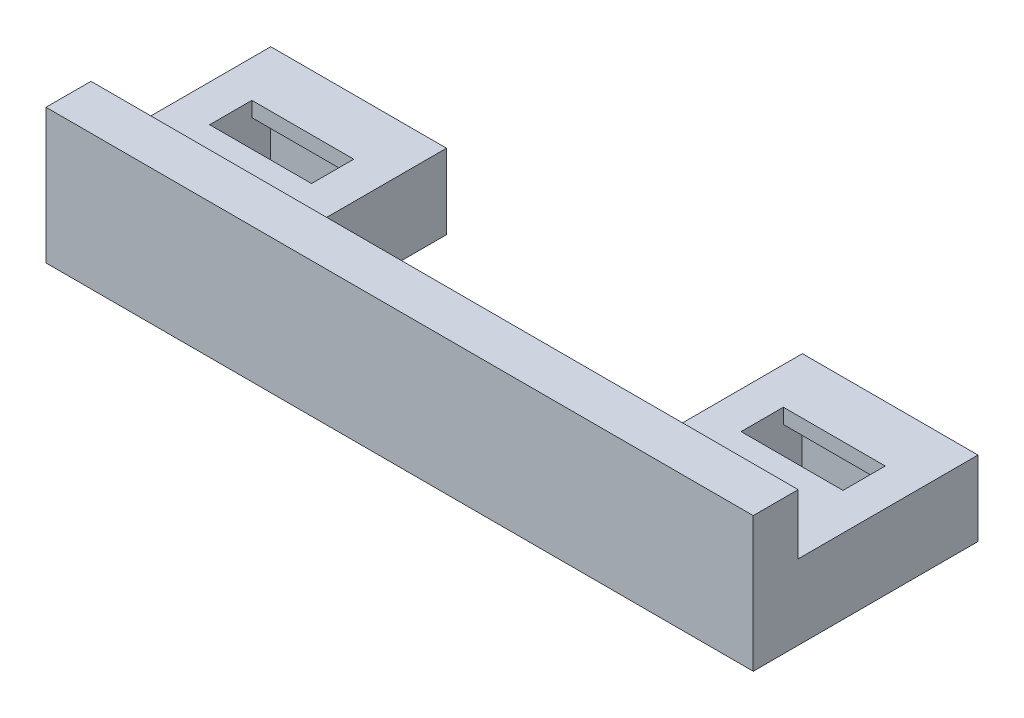
SolidWorks part; units mm, degrees
ref_plane "Front Plane" through (0, 0, 0) normal (0, 0, 1) x (1, 0, 0)
ref_plane "Top Plane" through (0, 0, 0) normal (0, 1, 0) x (1, 0, 0)
ref_plane "Right Plane" through (0, 0, 0) normal (1, 0, 0) x (0, 0, -1)
sketch "Sketch1" plane through (0, 0, 0) normal (0, 1, 0) x (1, 0, 0)
  line L1 (-59.4224, 28.5586) -> (0.5216, 28.5586)
  line L2 (-59.4224, 28.5586) -> (-59.4224, 9.5086)
  line L3 (-59.4224, 9.5086) -> (0.5216, 9.5086)
  line L4 (0.5216, 28.5586) -> (0.5216, 9.5086)
  line L13 (-47.6495, 18.6526) -> (-56.2855, 18.6526)
  line L14 (-47.6495, 18.6526) -> (-47.6495, 25.409)
  line L15 (-47.6495, 25.409) -> (-56.2855, 25.409)
  line L16 (-56.2855, 18.6526) -> (-56.2855, 25.409)
  line L17 (-11.2386, 18.6526) -> (-2.6026, 18.6526)
  line L18 (-11.2386, 18.6526) -> (-11.2386, 25.409)
  line L19 (-11.2386, 25.409) -> (-2.6026, 25.409)
  line L20 (-2.6026, 18.6526) -> (-2.6026, 25.409)
  dimension "D1" = 59.944
  dimension "D2" = 19.05
extrude "Boss-Extrude1" add sketch "Sketch1" along normal blind 5.08
sketch "Sketch2" plane through (0, 5.08, 0) normal (0, 1, 0) x (1, 0, 0)
  line L1 (-59.4224, 9.5086) -> (0.5216, 9.5086)
  line L2 (-59.4224, 9.5086) -> (-59.4224, 28.5586)
  line L3 (-59.4224, 28.5586) -> (0.5216, 28.5586)
  line L4 (0.5216, 9.5086) -> (0.5216, 28.5586)
  line L5 (-56.2855, 25.409) -> (-56.2855, 18.6526) construction
  line L6 (-56.2855, 23.8215) -> (-47.6495, 23.8215)
  line L7 (-56.2855, 23.8215) -> (-56.2855, 20.2401)
  line L8 (-11.2386, 25.409) -> (-11.2386, 18.6526) construction
  line L9 (-56.2855, 20.2401) -> (-47.6495, 20.2401)
  line L19 (-47.6495, 23.8215) -> (-47.6495, 20.2401)
  line L28 (-11.2386, 23.8215) -> (-2.6026, 23.8215)
  line L29 (-11.2386, 23.8215) -> (-11.2386, 20.2401)
  line L30 (-11.2386, 20.2401) -> (-2.6026, 20.2401)
  line L31 (-2.6026, 23.8215) -> (-2.6026, 20.2401)
extrude "Boss-Extrude2" add sketch "Sketch2" along normal blind 1.27
sketch "Sketch4" plane through (0, 0, 0) normal (0, -1, 0) x (1, 0, 0)
  line L5 (-9.5664, -25.0308) -> (-4.2749, -25.0308)
  line L6 (-9.5664, -19.0308) -> (-4.2749, -19.0308)
  line L7 (-54.6133, -25.0308) -> (-49.3218, -25.0308)
  line L8 (-54.6133, -19.0308) -> (-49.3218, -19.0308)
  circle A0 centre (-6.9206, -22.0308) radius 4 construction
  circle A1 centre (-51.9675, -22.0308) radius 4 construction
sketch "Sketch5" plane through (0, 0, 0) normal (0, -1, 0) x (1, 0, 0)
  line L5 (0.5216, -28.5586) -> (-59.4224, -28.5586) construction
  line L13 (-14.3628, -28.5586) -> (-44.5253, -28.5586)
  line L14 (-14.3628, -28.5586) -> (-14.3628, -15.5284)
  line L15 (-14.3628, -15.5284) -> (-44.5253, -15.5284)
  line L16 (-44.5253, -28.5586) -> (-44.5253, -15.5284)
extrude "Cut-Extrude1" cut sketch "Sketch5" against normal blind 30.48
sketch "Sketch6" plane through (0, 6.35, 0) normal (0, 1, 0) x (1, 0, 0)
  line L0 (0.5216, 9.5086) -> (0.5216, 28.5586) construction
  line L1 (-59.4224, 9.5086) -> (0.5216, 9.5086)
  line L2 (-59.4224, 9.5086) -> (-59.4224, 13.3186)
  line L3 (-59.4224, 13.3186) -> (0.5216, 13.3186)
  line L4 (0.5216, 9.5086) -> (0.5216, 13.3186)
extrude "Boss-Extrude4" add sketch "Sketch6" along normal blind 5.08
